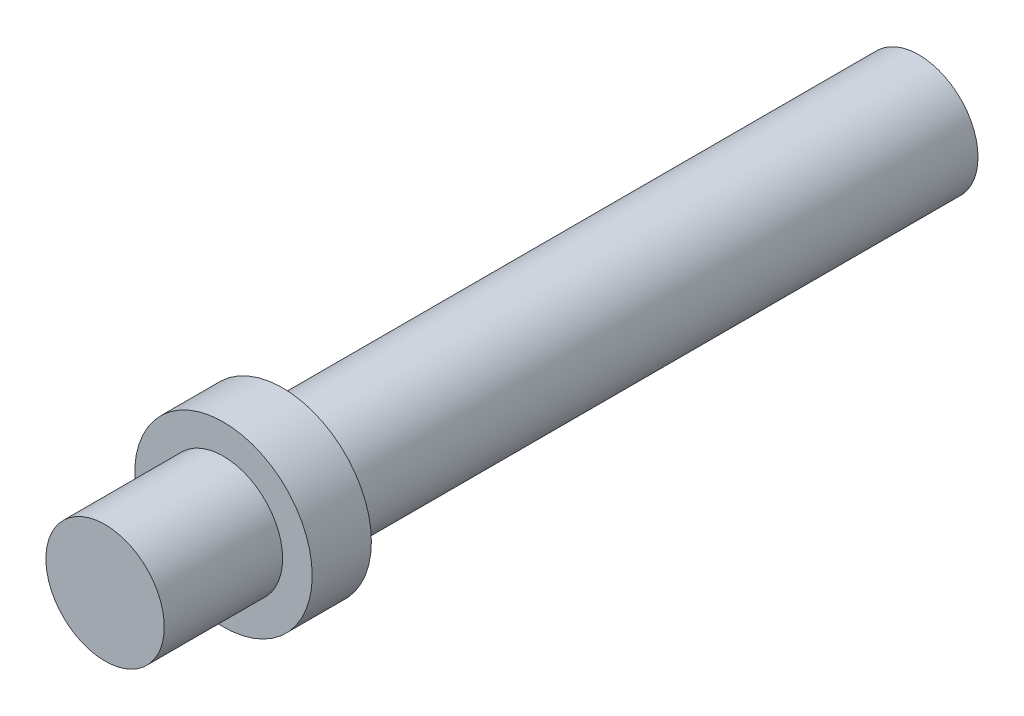
SolidWorks part; units mm, degrees
ref_plane "Alzado" through (0, 0, 0) normal (0, 0, 1) x (1, 0, 0)
ref_plane "Planta" through (0, 0, 0) normal (0, 1, 0) x (1, 0, 0)
ref_plane "Vista lateral" through (0, 0, 0) normal (1, 0, 0) x (0, 0, -1)
sketch "Croquis1" plane through (0, 0, 0) normal (1, 0, 0) x (0, 0, -1)
  line L0 (0, 0) -> (27.5, 0)
  line L1 (0, 0) -> (0, 2)
  line L2 (0, 2) -> (4, 2)
  line L3 (4, 2) -> (4, 3)
  line L4 (4, 3) -> (6, 3)
  line L5 (6, 3) -> (6, 2)
  line L6 (6, 2) -> (27.5, 2)
  line L7 (27.5, 2) -> (27.5, 0)
  dimension "D1" = 2
  dimension "D2" = 4
  dimension "D3" = 1
  dimension "D4" = 2
  dimension "D6" = 21.5
revolve "Revolución1" add sketch "Croquis1" angle 360 about L0
